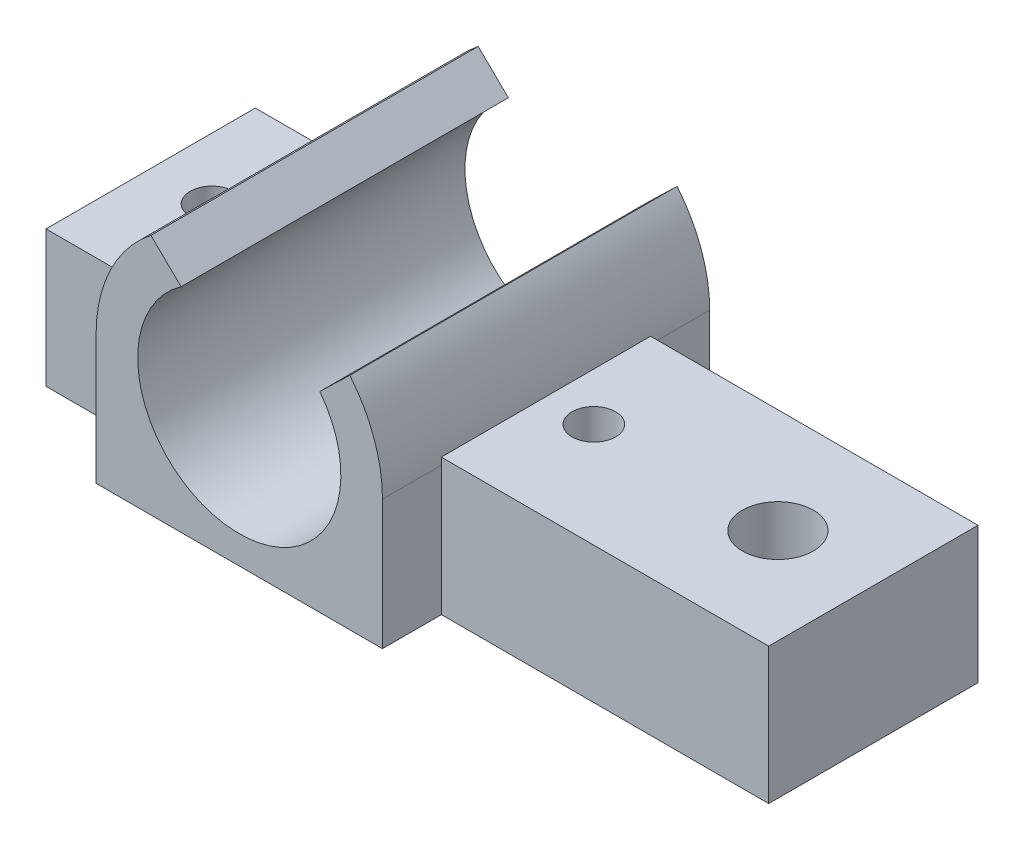
SolidWorks part; units mm, degrees
ref_plane "Front Plane" through (0, 0, 0) normal (0, 0, 1) x (1, 0, 0)
ref_plane "Top Plane" through (0, 0, 0) normal (0, 1, 0) x (1, 0, 0)
ref_plane "Right Plane" through (0, 0, 0) normal (1, 0, 0) x (0, 0, -1)
sketch "Sketch1" plane through (0, 0, 0) normal (0, 1, 0) x (1, 0, 0)
  line L0 (73.3937, 7.675) -> (73.3937, -7.675)
  line L1 (66.3937, 4.6765) -> (62.3437, 2.3383) construction
  line L2 (62.3437, 2.3383) -> (62.3437, -2.3383) construction
  line L3 (62.3437, -2.3383) -> (66.3937, -4.6765) construction
  line L4 (66.3937, -4.6765) -> (70.4437, -2.3383) construction
  line L5 (70.4437, -2.3383) -> (70.4437, 2.3383) construction
  line L6 (70.4437, 2.3383) -> (66.3937, 4.6765) construction
  line L7 (73.3937, -7.675) -> (20.3937, -7.675)
  line L9 (73.3937, 7.675) -> (20.3937, 7.675)
  line L10 (20.3937, -7.675) -> (20.3937, 7.675)
  line L11 (73.3937, -4.8412) -> (20.3937, 7.675) construction
  line L12 (73.3937, 4.8412) -> (20.3937, -7.675) construction
  circle A0 centre (52.8937, 0) radius 1.6
  circle A1 centre (24.8937, 0) radius 1.6
  circle A2 centre (66.3937, 0) radius 2.6
  circle A3 centre (66.3937, 0) radius 4.6765 construction
  dimension "D1" = 3.2
  dimension "D2" = 3.2
  dimension "D3" = 28
  dimension "D4" = 5.2
  dimension "D5" = 13.5
  dimension "D7" = 4.5
  dimension "D8" = 7
  dimension "D9" = 7.675
  dimension "D10" = 7.675
  dimension "D6" = 8.1
extrude "Boss-Extrude1" add sketch "Sketch1" along normal blind 10
sketch "Sketch2" plane through (0, 0, -7.675) normal (0, 0, -1) x (-1, 0, 0)
  line L3 (-23.2937, 10) -> (-26.4937, 10) construction
  line L4 (-23.2937, 10) -> (-26.4937, 10)
  line L5 (-24.8937, 10) -> (-24.8937, 21.3762)
  line L7 (-44.8016, 14.0386) -> (-47.0023, 16.171)
  line L8 (-34.6284, 15.6081) -> (-32.4128, 17.7612)
  line L12 (-49.3937, 0) -> (-28.3937, 0)
  line L13 (-28.3937, 9.5) -> (-28.3937, 0)
  line L15 (-49.3937, 9.5) -> (-49.3937, 0)
  arc A0 (-44.8016, 14.0386) -> (-34.6284, 15.6081) centre (-38.8937, 9.5) ccw
  arc A1 (-47.0023, 16.171) -> (-49.3937, 9.5) centre (-38.8937, 9.5) ccw
  arc A2 (-28.3937, 9.5) -> (-32.4128, 17.7612) centre (-38.8937, 9.5) ccw
  dimension "D1" = 14.9
  dimension "D2" = 14
  dimension "D4" = 21
extrude "Boss-Extrude2" add sketch "Sketch2" along normal blind 4.325 and the other way offset from surface (19.675 mm away) 4.325 contours A2 L8 A0 L7 A1 L15 L12 L13 other way up to face at (46.8937, 5, 7.675)
sketch "Sketch3" plane through (0, 0, 7.675) normal (0, 0, 1) x (1, 0, 0)
  line L1 (46.3269, 10) -> (31.4605, 10)
  line L2 (46.3269, 10) -> (31.4605, 10)
  arc A1 (31.4605, 10) -> (46.3269, 10) centre (38.8937, 9.5) ccw
  arc A2 (31.4605, 10) -> (46.3269, 10) centre (38.8937, 9.5) ccw
  dimension "D1" = 0
extrude "Cut-Extrude1" cut sketch "Sketch3" against normal through all
sketch "Sketch4" plane through (0, 0, 0) normal (0, -1, 0) x (1, 0, 0)
  line L1 (62.3667, 2.325) -> (62.3667, -2.325)
  line L2 (62.3667, -2.325) -> (66.3937, -4.65)
  line L3 (66.3937, -4.65) -> (70.4208, -2.325)
  line L4 (70.4208, -2.325) -> (70.4208, 2.325)
  line L5 (70.4208, 2.325) -> (66.3937, 4.65)
  line L6 (66.3937, 4.65) -> (62.3667, 2.325)
  circle A0 centre (66.3937, 0) radius 4.65 construction
  dimension "D1" = 9.3
extrude "Cut-Extrude2" cut sketch "Sketch4" against normal blind 4
sketch "Sketch5" plane through (0, 4, 0) normal (0, -1, 0) x (1, 0, 0)
  circle A0 centre (66.3937, 0) radius 2.6 construction
  circle A1 centre (66.3937, 0) radius 2.6
extrude "Boss-Extrude3" add sketch "Sketch5" against normal blind 0.4
